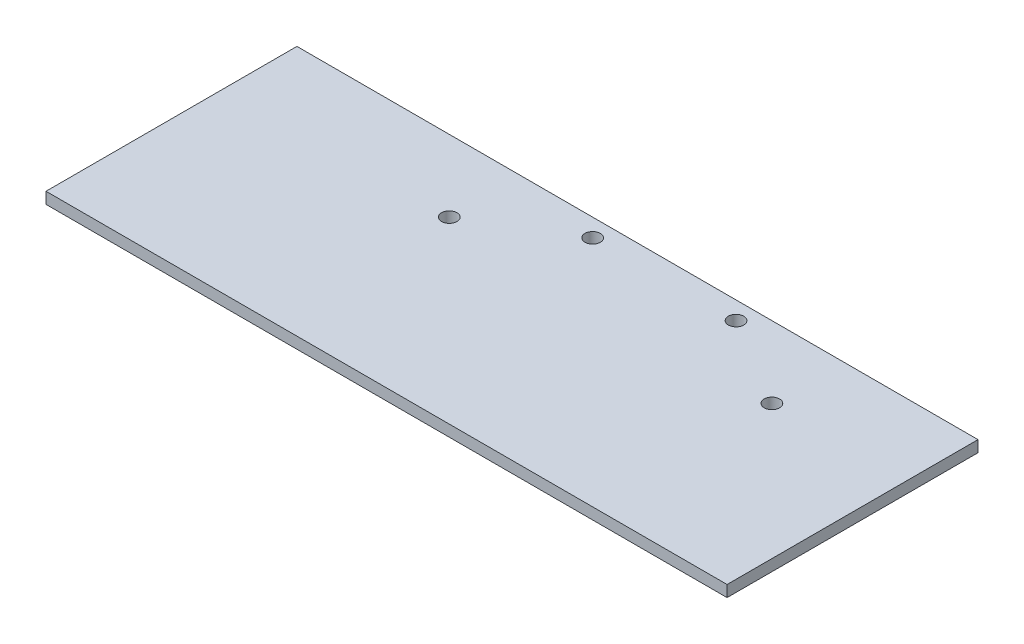
SolidWorks part; units mm, degrees
ref_plane "Front Plane" through (0, 0, 0) normal (0, 0, 1) x (1, 0, 0)
ref_plane "Top Plane" through (0, 0, 0) normal (0, 1, 0) x (1, 0, 0)
ref_plane "Right Plane" through (0, 0, 0) normal (1, 0, 0) x (0, 0, -1)
sketch "Sketch1" plane through (0, 0, 0) normal (0, 1, 0) x (1, 0, 0)
  line L1 (-107.5, -65) -> (82.5, -65)
  line L2 (-107.5, -65) -> (-107.5, 5)
  line L3 (-107.5, 5) -> (82.5, 5)
  line L4 (82.5, -65) -> (82.5, 5)
  line L5 (-107.5, -65) -> (82.5, 5) construction
  line L6 (-107.5, 5) -> (82.5, -65) construction
  circle A0 centre (-20, 0) radius 2.15
  circle A1 centre (20, 0) radius 2.15
  circle A2 centre (45, -15) radius 2.15
  circle A3 centre (-45, -15) radius 2.15
  point P8 (34.259, 0)
  point P10 (-39.7945, 0)
  point P11 (-12.5, -30)
  dimension "D4" = 4.3
  dimension "D5" = 4.3
  dimension "D6" = 4.3
  dimension "D7" = 4.3
  dimension "D1" = 15
  dimension "D2" = 25
  dimension "D3" = 25
  dimension "D8" = 30
  dimension "D9" = 12.5
  dimension "D10" = 190
  dimension "D11" = 70
  dimension "D12" = 20
  dimension "D13" = 20
extrude "Boss-Extrude1" add sketch "Sketch1" along normal mid plane 3.175
